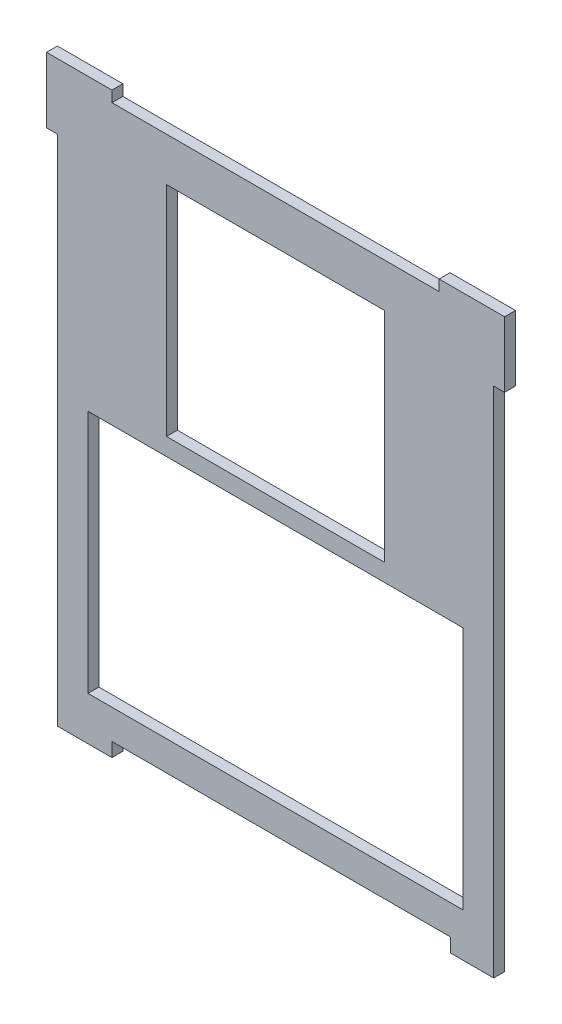
SolidWorks part; units mm, degrees
ref_plane "Front" through (0, 0, 0) normal (0, 0, 1) x (1, 0, 0)
ref_plane "Top" through (0, 0, 0) normal (0, 1, 0) x (1, 0, 0)
ref_plane "Right" through (0, 0, 0) normal (1, 0, 0) x (0, 0, -1)
sketch "Sketch1" plane through (0, 0, 0) normal (0, 0, 1) x (1, 0, 0)
  line L1 (63.5, -88.9) -> (-63.5, -88.9)
  line L2 (63.5, -88.9) -> (63.5, 88.9)
  line L3 (63.5, 88.9) -> (-63.5, 88.9)
  line L4 (-63.5, -88.9) -> (-63.5, 88.9)
  line L5 (63.5, -88.9) -> (-63.5, 88.9) construction
  line L6 (63.5, 88.9) -> (-63.5, -88.9) construction
  point P0 (0, 0)
  dimension "D1" = 177.8
  dimension "D2" = 127
extrude "Boss-Extrude1" add sketch "Sketch1" along normal blind 3.175
sketch "Sketch3" plane through (0, 0, 3.175) normal (0, 0, 1) x (1, 0, 0)
  line L0 (-63.5, 0) -> (63.5, 0) construction
  line L1 (-63.5, 88.9) -> (-63.5, -88.9) construction
  line L2 (63.5, -88.9) -> (63.5, 88.9) construction
  line L3 (0, 0) -> (0, 88.9) construction
  line L4 (63.5, 88.9) -> (-63.5, 88.9) construction
  line L5 (0, -63.5) -> (0, -88.9) construction
  line L6 (-63.5, -88.9) -> (63.5, -88.9) construction
  line L7 (0, 12.7) -> (0, 0) construction
  line L8 (31.75, 12.7) -> (-31.75, 12.7)
  line L9 (31.75, 12.7) -> (31.75, 76.2)
  line L10 (31.75, 76.2) -> (-31.75, 76.2)
  line L11 (-31.75, 12.7) -> (-31.75, 76.2)
  line L12 (31.75, 12.7) -> (-31.75, 76.2) construction
  line L13 (31.75, 76.2) -> (-31.75, 12.7) construction
  line L14 (54.61, -63.5) -> (-54.61, -63.5)
  line L15 (54.61, -63.5) -> (54.61, 7.62)
  line L16 (54.61, 7.62) -> (-54.61, 7.62)
  line L17 (-54.61, -63.5) -> (-54.61, 7.62)
  line L18 (54.61, -63.5) -> (-54.61, 7.62) construction
  line L19 (54.61, 7.62) -> (-54.61, -63.5) construction
  line L20 (0, 76.2) -> (0, 88.9) construction
  point P10 (0, 44.45)
  point P18 (0, -27.94)
  dimension "D1" = 63.5
  dimension "D2" = 63.5
  dimension "D3" = 71.12
  dimension "D4" = 109.22
  dimension "D7" = 5.08
extrude "Cut-Extrude2" cut sketch "Sketch3" against normal through all
sketch "Sketch4" plane through (0, 0, 3.175) normal (0, 0, 1) x (1, 0, 0)
  line L3 (-60.325, 92.075) -> (-66.675, 92.075)
  line L4 (-66.675, 85.725) -> (-66.675, 92.075)
  line L5 (-60.325, 85.725) -> (-66.675, 92.075) construction
  line L6 (-60.325, 92.075) -> (-66.675, 85.725) construction
  line L9 (60.325, 92.075) -> (66.675, 92.075)
  line L10 (66.675, 85.725) -> (66.675, 92.075)
  line L11 (60.325, 85.725) -> (66.675, 92.075) construction
  line L12 (60.325, 92.075) -> (66.675, 85.725) construction
  line L14 (-66.675, 85.725) -> (-66.675, 73.025)
  line L15 (-66.675, 73.025) -> (-60.325, 73.025)
  line L16 (-60.325, 85.725) -> (-60.325, 73.025)
  line L17 (-60.325, 92.075) -> (-47.625, 92.075)
  line L19 (-60.325, 85.725) -> (-47.625, 85.725)
  line L20 (-47.625, 92.075) -> (-47.625, 85.725)
  line L21 (60.325, 85.725) -> (47.625, 85.725)
  line L23 (60.325, 92.075) -> (47.625, 92.075)
  line L24 (47.625, 85.725) -> (47.625, 92.075)
  line L26 (60.325, 85.725) -> (60.325, 73.025)
  line L27 (60.325, 73.025) -> (66.675, 73.025)
  line L28 (66.675, 85.725) -> (66.675, 73.025)
  point P0 (-63.5, 88.9)
  point P5 (63.5, 88.9)
  dimension "D1" = 6.35
  dimension "D2" = 6.35
  dimension "D3" = 6.35
  dimension "D4" = 6.35
  dimension "D5" = 12.7
  dimension "D6" = 12.7
  dimension "D7" = 12.7
  dimension "D8" = 12.7
extrude "Boss-Extrude2" add sketch "Sketch4" against normal blind 3.175
sketch "Sketch5" plane through (0, 0, 3.175) normal (0, 0, 1) x (1, 0, 0)
  line L1 (-63.5, -88.9) -> (-44.45, -88.9)
  line L2 (-63.5, -88.9) -> (-63.5, -76.2)
  line L3 (-63.5, -76.2) -> (-44.45, -76.2)
  line L4 (-44.45, -88.9) -> (-44.45, -76.2)
  line L5 (63.5, -88.9) -> (44.45, -88.9)
  line L6 (63.5, -88.9) -> (63.5, -76.2)
  line L7 (63.5, -76.2) -> (44.45, -76.2)
  line L8 (44.45, -88.9) -> (44.45, -76.2)
  dimension "D1" = 19.05
  dimension "D2" = 19.05
  dimension "D3" = 12.7
  dimension "D4" = 12.7
extrude "Cut-Extrude3" cut sketch "Sketch5" against normal up to next
sketch "Sketch6" plane through (0, 0, 3.175) normal (0, 0, 1) x (1, 0, 0)
  line L0 (-44.45, -88.9) -> (-44.45, -76.2)
  line L1 (-44.45, -88.9) -> (-41.148, -88.9)
  line L2 (-44.45, -76.2) -> (-41.148, -76.2)
  line L3 (-41.148, -88.9) -> (-41.148, -76.2)
  dimension "D1" = 3.302
extrude "Cut-Extrude4" cut sketch "Sketch6" against normal through all
sketch "Sketch7" plane through (0, 0, 3.175) normal (0, 0, 1) x (1, 0, 0)
  line L1 (-41.148, -76.2) -> (-41.148, -72.136)
  line L2 (44.45, -76.2) -> (44.45, -72.136)
  line L3 (-41.148, -72.136) -> (44.45, -72.136)
  line L4 (-41.148, -76.2) -> (-41.148, -88.9)
  line L5 (-41.148, -88.9) -> (44.45, -88.9)
  line L6 (44.45, -88.9) -> (44.45, -76.2)
  dimension "D1" = 4.064
extrude "Cut-Extrude5" cut sketch "Sketch7" against normal through all
sketch "Sketch9" plane through (0, 0, 3.175) normal (0, 0, 1) x (1, 0, 0)
  line L0 (-41.148, -76.2) -> (-41.148, -72.136)
  line L1 (-41.148, -76.2) -> (-47.625, -76.2)
  line L2 (-41.148, -72.136) -> (-47.625, -72.136)
  line L3 (-47.625, -76.2) -> (-47.625, -72.136)
  line L4 (1.651, -72.136) -> (1.651, 88.9) construction
  line L5 (44.45, -72.136) -> (-41.148, -72.136) construction
  line L6 (47.625, 88.9) -> (-47.625, 88.9) construction
  line L7 (44.45, -76.2) -> (44.45, -72.136)
  line L8 (44.45, -72.136) -> (50.927, -72.136)
  line L9 (44.45, -76.2) -> (50.927, -76.2)
  line L10 (50.927, -76.2) -> (50.927, -72.136)
  dimension "D1" = 6.477
extrude "Cut-Extrude6" cut sketch "Sketch9" against normal through all
